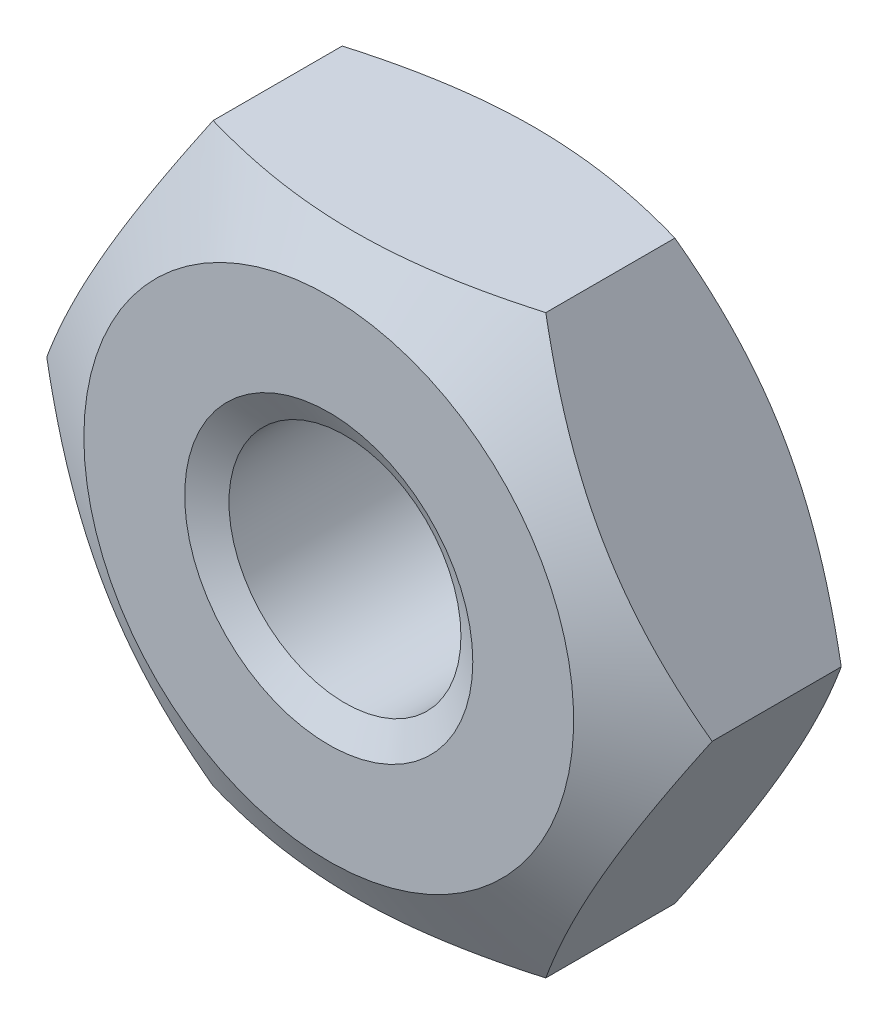
SolidWorks part; units mm, degrees
ref_plane "Front" through (0, 0, 0) normal (0, 0, 1) x (1, 0, 0)
ref_plane "Top" through (0, 0, 0) normal (0, 1, 0) x (1, 0, 0)
ref_plane "Right" through (0, 0, 0) normal (1, 0, 0) x (0, 0, -1)
sketch "Sketch1" plane through (0, 0, 0) normal (0, 0, 1) x (1, 0, 0)
  line L1 (2.8868, 0) -> (1.4434, 2.5)
  line L2 (1.4434, 2.5) -> (-1.4434, 2.5)
  line L3 (-1.4434, 2.5) -> (-2.8868, 0)
  line L4 (-2.8868, 0) -> (-1.4434, -2.5)
  line L5 (-1.4434, -2.5) -> (1.4434, -2.5)
  line L6 (1.4434, -2.5) -> (2.8868, 0)
  circle A0 centre (0, 0) radius 2.5 construction
  circle A1 centre (0, 0) radius 1.0065
  dimension "D" = 2.013
  dimension "s" = 5
extrude "BaseNut" add sketch "Sketch1" against normal blind 2
cosmetic thread "ThreadCosmetic1" [suppressed] parameters "D"=2.5
sketch "Sketch2" plane through (0, 0, 0) normal (0, 1, 0) x (1, 0, 0)
  line L0 (-2.8868, 2) -> (-2.125, 2)
  line L2 (-2.125, 2) -> (-2.8868, 1.5602)
  line L3 (-2.8868, 1.5602) -> (-2.8868, 2)
  line L4 (0, 3.3759) -> (0, -9.8171) construction
  line L6 (-9.7712, 1) -> (9.8853, 1) construction
  line L7 (-2.8868, 0.4398) -> (-2.8868, 0)
  line L8 (-2.125, 0) -> (-2.8868, 0.4398)
  line L9 (-2.8868, 0) -> (-2.125, 0)
  dimension "dw" = 4.25
  dimension "D1" = 30
  dimension "D2" = 1
revolve "Double-Chamfer" cut sketch "Sketch2" angle 360 about L4
chamfer "EndChamfer" distance 0.2435 angle 30 2 edges at (1.0065, 0, -2) (1.0065, 0, 0)
sketch "Sketch3" plane through (0, 0, 0) normal (0, 1, 0) x (1, 0, 0)
  line L0 (-1.2174, 1.7565) -> (-1.0065, 1.6347)
  line L1 (-1.0065, 1.6347) -> (-0.763, 1.6347)
  line L2 (-0.763, 1.6347) -> (-0.763, 1.8782)
  line L3 (-0.763, 1.8782) -> (-1.0065, 1.8782)
  line L4 (-1.0065, 1.8782) -> (-1.2174, 1.7565)
  line L5 (0, 7.4383) -> (0, 16.8806) construction
  dimension "D1" = 0.2435
  dimension "D2" = 2.013
revolve "Cut-Revolve10" [suppressed] cut sketch "Sketch3" angle 360 about L5
pattern_linear "LPattern10" [suppressed] count 7 spacing 0.2922 along (0, 0, -1)
equation "\"dw@Sketch2\" = \"s@Sketch1\"-0.75"
equation "\"D2@Sketch2\" = \"m@BaseNut\" / 2"
equation "\"D2@Sketch3\" = \"D@Sketch1\""
equation "\"D1@Sketch3\" =  (\"D@ThreadCosmetic1\"   - \"D@Sketch1\")  / 2"
equation "\"D3@LPattern10\" = \"D1@Sketch3\" * 1.2"
equation "\"D1@LPattern10\" = \"m@BaseNut\"/\"D3@LPattern10\""
